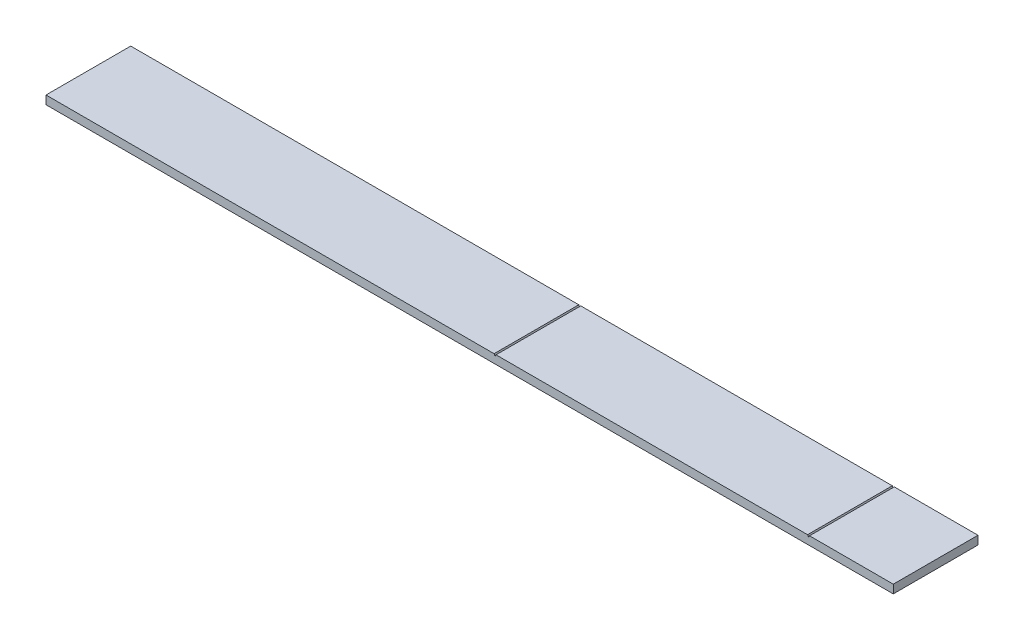
SolidWorks part; units mm, degrees
ref_plane "Front" through (0, 0, 0) normal (0, 0, 1) x (1, 0, 0)
ref_plane "Top" through (0, 0, 0) normal (0, 1, 0) x (1, 0, 0)
ref_plane "Right" through (0, 0, 0) normal (1, 0, 0) x (0, 0, -1)
sketch "Sketch1" plane through (0, 0, 0) normal (0, 0, 1) x (1, 0, 0)
  line L0 (530, 0) -> (530, -2) construction
  line L1 (0, 0) -> (528.8453, 0)
  line L2 (0, 0) -> (0, -10)
  line L3 (0, -10) -> (1000, -10)
  line L4 (1000, 0) -> (1000, -10)
  line L5 (900, 0) -> (900, -2) construction
  line L6 (528.8453, 0) -> (530, -2)
  line L7 (530, -2) -> (531.1547, 0)
  line L8 (898.8453, 0) -> (900, -2)
  line L9 (900, -2) -> (901.1547, 0)
  line L10 (531.1547, 0) -> (898.8453, 0)
  line L11 (901.1547, 0) -> (1000, 0)
  point P4 (530, 0)
  point P5 (900, 0)
  dimension "D1" = 10
  dimension "D2" = 1000
  dimension "D3" = 530
  dimension "D4" = 900
  dimension "D5" = 60
  dimension "D6" = 60
  dimension "D7" = 60
  dimension "D8" = 60
  dimension "D9" = 2
  dimension "D10" = 2
extrude "Boss-Extrude1" add sketch "Sketch1" along normal blind 100
